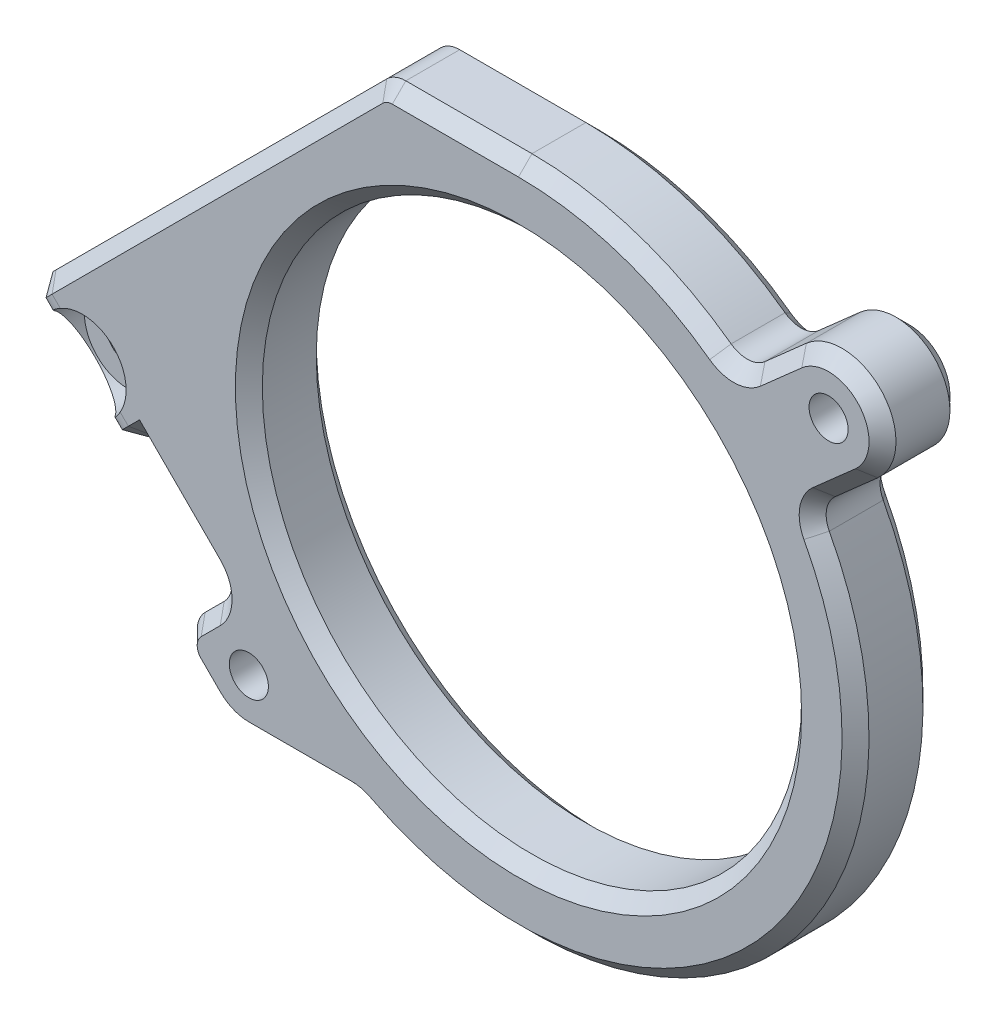
SolidWorks part; units mm, degrees
ref_plane "正面" through (0, 0, 0) normal (0, 0, 1) x (1, 0, 0)
ref_plane "平面" through (0, 0, 0) normal (0, 1, 0) x (1, 0, 0)
ref_plane "右側面" through (0, 0, 0) normal (1, 0, 0) x (0, 0, -1)
sketch "ｽｹｯﾁ1" plane through (0, 0, 0) normal (0, 0, 1) x (1, 0, 0)
  line L1 (30, -27.5) -> (-30, -27.5)
  line L2 (30, -27.5) -> (30, 27.5)
  line L3 (30, 27.5) -> (-30, 27.5)
  line L4 (-30, -27.5) -> (-30, 27.5)
  line L5 (30, -27.5) -> (-30, 27.5) construction
  line L6 (30, 27.5) -> (-30, -27.5) construction
  point P0 (0, 0)
  dimension "D1" = 55
  dimension "D2" = 60
extrude "ﾎﾞｽ - 押し出し1" add sketch "ｽｹｯﾁ1" along normal blind 6
sketch "ｽｹｯﾁ2" plane through (0, 0, 6) normal (0, 0, 1) x (1, 0, 0)
  line L0 (23, 20) -> (-20, -18)
  point P2 (0, 0)
  dimension "D1" = 18
  dimension "D2" = 20
  dimension "D3" = 43
  dimension "D4" = 38
hole_wizard "M4 すきま穴1" positions "ｽｹｯﾁ3" profile "ｽｹｯﾁ4" hole size "M4" standard "ISO"
sketch "ｽｹｯﾁ3" plane through (0, 0, 6) normal (0, 0, 1) x (1, 0, 0)
  point P0 (-20, -18)
  point P3 (23, 20)
sketch "ｽｹｯﾁ4" plane through (-20, -18, 6) normal (1, 0, 0) x (0, -1, 0)
  line L0 (0, 0) -> (0, 10)
  line L1 (0, 10) -> (1.45, 10)
  line L2 (1.45, 10) -> (1.45, 0)
  line L5 (1.45, 0) -> (0, 0)
  line L10 (0, 10) -> (-1.45, 10) construction
  line L11 (0, -6.35) -> (0, 107.95) construction
  dimension "穴の直径" = 2.9
  dimension "穴の深さ" = 10
  dimension "ﾄﾞﾘﾙ角度" = 180
sketch "ｽｹｯﾁ5" plane through (0, 0, 6) normal (0, 0, 1) x (1, 0, 0)
  circle A0 centre (0, 0) radius 20
  dimension "D1" = 40
extrude "ｶｯﾄ - 押し出し1" cut sketch "ｽｹｯﾁ5" against normal through all
sketch "ｽｹｯﾁ6" plane through (0, 0, 6) normal (0, 0, 1) x (1, 0, 0)
  line L0 (-20, -18) -> (23, 20) construction
  line L1 (23, 20) -> (-20, -18) construction
  line L2 (-22.6488, -15.0027) -> (20.3512, 22.9973)
  line L3 (-17.3512, -20.9973) -> (25.6488, 17.0027)
  line L8 (-30, 27.5) -> (-30, -27.5)
  line L9 (-30, -27.5) -> (30, -27.5)
  line L10 (30, -27.5) -> (30, 27.5)
  line L11 (30, 27.5) -> (-30, 27.5)
  line L12 (-30, 27.5) -> (-30, -27.5)
  line L13 (-30, -27.5) -> (30, -27.5)
  line L14 (30, -27.5) -> (30, 27.5)
  line L15 (30, 27.5) -> (-30, 27.5)
  circle A0 centre (0, 0) radius 20 construction
  circle A1 centre (0, 0) radius 20
  arc A2 (-22.6488, -15.0027) -> (-17.3512, -20.9973) centre (-20, -18) ccw
  arc A3 (25.6488, 17.0027) -> (20.3512, 22.9973) centre (23, 20) ccw
  circle A4 centre (0, 0) radius 25
  point P8 (1.5, 1)
  dimension "D2" = 50
  dimension "D1" = 8
  dimension "D3" = 0
extrude "ｶｯﾄ - 押し出し2" cut sketch "ｽｹｯﾁ6" against normal through all contours L13 L14 L15 L12 | A4 | A2 L3 A3 L2
sketch "ｽｹｯﾁ7" plane through (0, 0, 6) normal (0, 0, 1) x (1, 0, 0)
  line L0 (0, 25) -> (-20, 25)
  line L1 (-20, -22) -> (-21.5, -22)
  line L2 (-20, -22) -> (-20, 25)
  line L3 (-20, 25) -> (-21.5, 25)
  line L4 (-21.5, -22) -> (-21.5, 25)
  line L5 (-20, -22) -> (-11.8743, -22)
  line L8 (-21.0078, -13.5525) -> (-22.6488, -15.0027)
  line L9 (-17.3512, -20.9973) -> (-15.651, -19.4948)
  line L10 (21.2717, 13.1345) -> (25.6488, 17.0027)
  line L11 (20.3512, 22.9973) -> (16.0334, 19.1815)
  line L12 (-21.0078, -13.5525) -> (-22.6488, -15.0027)
  line L13 (-17.3512, -20.9973) -> (-15.651, -19.4948)
  line L14 (21.2717, 13.1345) -> (25.6488, 17.0027)
  line L15 (20.3512, 22.9973) -> (16.0334, 19.1815)
  arc A0 (-22.6488, -15.0027) -> (-17.3512, -20.9973) centre (-20, -18) ccw construction
  arc A5 (-22.6488, -15.0027) -> (-17.3512, -20.9973) centre (-20, -18) ccw
  arc A6 (-15.651, -19.4948) -> (21.2717, 13.1345) centre (0, 0) ccw
  arc A7 (25.6488, 17.0027) -> (20.3512, 22.9973) centre (23, 20) ccw
  arc A8 (16.0334, 19.1815) -> (-21.0078, -13.5525) centre (0, 0) ccw
  arc A9 (-22.6488, -15.0027) -> (-17.3512, -20.9973) centre (-20, -18) ccw
  arc A10 (-15.651, -19.4948) -> (21.2717, 13.1345) centre (0, 0) ccw
  arc A11 (25.6488, 17.0027) -> (20.3512, 22.9973) centre (23, 20) ccw
  arc A12 (16.0334, 19.1815) -> (-21.0078, -13.5525) centre (0, 0) ccw
  line M17 (-21.0078, -13.5525) -> (-22.6488, -15.0027)
  arc M18 (-22.6488, -15.0027) -> (-17.3512, -20.9973) centre (-20, -18) ccw
  line M19 (-17.3512, -20.9973) -> (-15.651, -19.4948)
  arc M20 (-15.651, -19.4948) -> (21.2717, 13.1345) centre (0, 0) ccw
  arc M24 (16.0334, 19.1815) -> (-21.0078, -13.5525) centre (0, 0) ccw
  dimension "D2" = 1.5
  dimension "D1" = 0
extrude "ﾎﾞｽ - 押し出し2" add sketch "ｽｹｯﾁ7" against normal up to surface (6 mm away) contours L4 L1 M18 M17 M24 | L4 L2 L3 M24 | L2 L0 M24 | L5 M18 M20 M19
sketch "ｽｹｯﾁ8" plane through (0, 0, 6) normal (0, 0, 1) x (1, 0, 0)
  line L0 (-20.9025, 25.5975) -> (-45.0784, 1.4216)
  line L1 (-45.0784, 1.4216) -> (-21.6569, -22)
  line L3 (-21.5, 12.7574) -> (-21.5, 25) construction
  line L4 (-20, -22) -> (-21.6569, -22)
  arc A1 (-22.6488, -15.0027) -> (-20, -22) centre (-20, -18) ccw construction
  point P3 (-22.5, -21)
  point P9 (-21.5, -22)
  point P10 (0, 0)
  point P11 (0, 0)
  point P13 (0, 0)
  point P15 (-21.5, -22)
  dimension "D1" = 45
extrude "ﾎﾞｽ - 押し出し3" add sketch "ｽｹｯﾁ8" against normal up to surface (6 mm away) up to face at (-3.845, 3.3122, 0)
sketch "ｽｹｯﾁ9" plane through (0, 0, 0) normal (0, 0, -1) x (-1, 0, 0)
  line L0 (32.3505, -11.3063) -> (25.2794, -4.2353)
  line L1 (22.8284, -20.8284) -> (45.0784, 1.4216) construction
  line L2 (25.2794, -4.2353) -> (38.0074, 8.4926)
  line L3 (45.0784, 1.4216) -> (21.5, 25) construction
  line M4 (22.8284, -20.8284) -> (45.0784, 1.4216)
  line M5 (45.0784, 1.4216) -> (21.5, 25)
  dimension "D1" = 10
  dimension "D2" = 18
extrude "ﾎﾞｽ - 押し出し4" add sketch "ｽｹｯﾁ9" along normal blind 4 contours L2 L0 M4 M5
sketch "ｽｹｯﾁ10" plane through (0, 0, -4) normal (0, 0, -1) x (-1, 0, 0)
  line L0 (32.3505, -11.3063) -> (25.2794, -4.2353) construction
  line L1 (25.2794, -4.2353) -> (38.0074, 8.4926) construction
  line L2 (38.0074, 8.4926) -> (21.5, 25) construction
  line L3 (21.5, 25) -> (0, 25) construction
  line L4 (-16.0334, 19.1815) -> (-20.3512, 22.9973) construction
  line L5 (-25.6488, 17.0027) -> (-21.2717, 13.1345) construction
  line L6 (11.8743, -22) -> (20, -22) construction
  line L8 (38.0074, 8.4926) -> (25.2794, -4.2353) construction
  line L9 (25.2794, -4.2353) -> (32.3505, -11.3063) construction
  line L10 (32.3505, -11.3063) -> (45.0784, 1.4216) construction
  line L11 (45.0784, 1.4216) -> (38.0074, 8.4926) construction
  line L12 (32.3505, -11.3063) -> (25.2794, -4.2353)
  line L13 (32.3505, 2.8358) -> (38.0074, 8.4926)
  line L14 (38.0074, 8.4926) -> (21.5, 25)
  line L15 (21.5, 25) -> (10.1863, 25)
  line L16 (-16.0334, 19.1815) -> (-20.3512, 22.9973)
  line L17 (-25.6488, 17.0027) -> (-21.2717, 13.1345)
  line L18 (11.8743, -22) -> (20, -22)
  line L20 (38.0074, 8.4926) -> (32.3505, 2.8358)
  line L21 (25.2794, -4.2353) -> (32.3505, -11.3063)
  line L22 (39.4216, -4.2353) -> (45.0784, 1.4216)
  line L23 (45.0784, 1.4216) -> (38.0074, 8.4926)
  line L24 (39.4216, -4.2353) -> (10.1863, 25)
  line L29 (38.0074, 8.4926) -> (25.2794, -4.2353)
  line L30 (25.2794, -4.2353) -> (32.3505, -11.3063)
  line L31 (32.3505, -11.3063) -> (45.0784, 1.4216)
  line L32 (45.0784, 1.4216) -> (38.0074, 8.4926)
  line L33 (38.0074, 8.4926) -> (32.3505, 2.8358)
  line L34 (25.2794, -4.2353) -> (32.3505, -11.3063)
  line L35 (32.3505, -11.3063) -> (45.0784, 1.4216)
  line L36 (45.0784, 1.4216) -> (38.0074, 8.4926)
  arc A0 (0, 25) -> (-16.0334, 19.1815) centre (0, 0) ccw construction
  arc A1 (-20.3512, 22.9973) -> (-25.6488, 17.0027) centre (-23, 20) ccw construction
  arc A2 (-21.2717, 13.1345) -> (11.8743, -22) centre (0, 0) ccw construction
  arc A3 (0, 25) -> (-16.0334, 19.1815) centre (0, 0) ccw
  arc A4 (-20.3512, 22.9973) -> (-25.6488, 17.0027) centre (-23, 20) ccw
  arc A5 (-21.2717, 13.1345) -> (11.8743, -22) centre (0, 0) ccw
  dimension "D1" = 8
  dimension "D2" = 0
extrude "ｶｯﾄ - 押し出し3" cut sketch "ｽｹｯﾁ10" against normal through all contours L14 L15 L24 L22 L23
sketch "ｽｹｯﾁ12" plane through (0, 0, 6) normal (0, 0, 1) x (1, 0, 0)
  line L0 (-39.4216, -4.2353) -> (-25.6569, -18)
  line L1 (-39.4216, -4.2353) -> (-35.1789, 0.0074)
  line L2 (-25.6569, -18) -> (-21.4142, -13.7574)
  line L3 (-35.1789, 0.0074) -> (-21.4142, -13.7574)
  line L4 (-39.4216, -4.2353) -> (-22.8284, -20.8284) construction
  circle A0 centre (-20, -18) radius 1.45 construction
  dimension "D1" = 4
  dimension "D2" = 6
extrude "ｶｯﾄ - 押し出し4" cut sketch "ｽｹｯﾁ12" against normal blind 6
fillet "ﾌｨﾚｯﾄ1" radius 2 3 edges at (-25.2794, -4.2353, -2) (-32.3505, 2.8358, -2) (-25.6569, -18, 3)
sketch "ｽｹｯﾁ13" plane through (0, 0, 0) normal (0, 0, 1) x (1, 0, 0)
  line L4 (-32.3505, -11.3063) -> (-28.1079, -7.0637)
  line L5 (-28.1079, -7.0637) -> (-35.1789, 0.0074)
  line L6 (-35.1789, 0.0074) -> (-39.4216, -4.2353)
  line L7 (-39.4216, -4.2353) -> (-32.3505, -11.3063)
  line L8 (-32.3505, -11.3063) -> (-28.1079, -7.0637)
  line L9 (-28.1079, -7.0637) -> (-35.1789, 0.0074)
  line L10 (-35.1789, 0.0074) -> (-39.4216, -4.2353)
  line L11 (-39.4216, -4.2353) -> (-32.3505, -11.3063)
  dimension "D1" = 0
extrude "ﾎﾞｽ - 押し出し5" add sketch "ｽｹｯﾁ13" along normal blind 6
chamfer "面取り2" distance 5 angle 45 1 edges at (-35.886, -7.7708, 6)
fillet "ﾌｨﾚｯﾄ4" radius 2 7 edges at (21.2717, 13.1345, 3) (16.0334, 19.1815, 3) (-10.1863, 25, 3) (-11.8743, -22, 3) (-21.4142, -13.7574, 3) (-35.886, -7.7708, 1) (-32.3505, -4.2353, 6)
chamfer "面取り3" distance 1 angle 45 53 edges at (-21.5307, -21.6955, 6) (-21.5307, -21.6955, 0) (-23.5355, -20.1213, 0) (-29.5221, -8.4779, -4) (-32.3505, -11.3063, -1.9142) (-35.886, -7.7708, -4) (-36.5931, -1.4069, -4) (-28.815, -0.6997, -4) (-32.3505, 2.0074, -4) (-26.1079, -4.2353, -4) (-23.5355, -15.8787, 6) (-23.5355, -15.8787, 0) (-23.5355, -20.1213, 6) (-24.8284, -18, 6) (-24.8284, -18, 0) (24.0713, 15.6086, 6) (24.0713, 15.6086, 0) (17.8053, -17.5491, 0) (17.8053, -17.5491, 6) (7.7717, 23.7613, 6) (7.7717, 23.7613, 0) (18.8154, 21.6401, 6) (18.8154, 21.6401, 0) (-39.4216, -4.2353, -1.9142) (-37.6538, -2.4675, 3.5) (-23.0362, 12.1501, 6) (-22.2684, 12.9179, 0) (-35.8414, -0.6552, 5.8478) (-39.3139, -4.1276, 0.9369) (-25.4681, -9.7034, 0) (-4.6789, 25, 0) (-16.1847, -22, 0) (-10.1232, 24.8478, 0) (-28.1685, -7.1244, 6) (-25.4681, -9.7034, 6) (-10.1232, 24.8478, 6) (-30.5827, -9.5386, 3.5) (-28.7704, -7.7262, 5.8478) (-32.2429, -11.1987, 0.9369) (21.8499, 13.0707, 0) (21.8499, 13.0707, 6) (16.0467, 19.7836, 0) (16.0467, 19.7836, 6) (-11.8979, -22.0563, 6) (-11.8979, -22.0563, 0) (-22.2426, -13.7574, 6) (-22.2426, -13.7574, 0) (20, 0, 0) (20, 0, 6) (25.9973, 22.6488, 0) (25.9973, 22.6488, 6) (-16.1847, -22, 6) (-4.6789, 25, 6)
sketch "ｽｹｯﾁ14" plane through (0, 0, 6) normal (0, 0, 1) x (1, 0, 0)
  line L0 (-31.7647, -3.6495) -> (-32.3505, -4.2353)
  line L11 (-34.5931, -0.8211) -> (-28.9363, -6.4779)
  line L21 (-34.5931, -0.8211) -> (-28.9363, -6.4779)
  line L50 (-33.0576, -10.5992) -> (-38.7145, -4.9424) construction
  line L87 (-10.065, 23.7071) -> (-34.5931, -0.8211)
  line L88 (-10.065, 23.7071) -> (-34.5931, -0.8211)
  line L89 (-28.9363, -6.4779) -> (-28.1079, -5.6495)
  line L90 (-28.9363, -6.4779) -> (-28.1079, -5.6495)
  line L91 (-28.1079, -5.6495) -> (-22.1213, -11.636)
  line L92 (-28.1079, -5.6495) -> (-22.1213, -11.636)
  line L93 (-22.1213, -15.8787) -> (-23.5355, -17.2929)
  line L94 (-22.1213, -15.8787) -> (-23.5355, -17.2929)
  line L95 (-23.5355, -18.7071) -> (-22.1213, -20.1213)
  line L96 (-23.5355, -18.7071) -> (-22.1213, -20.1213)
  line L97 (-20, -21) -> (-12.3693, -21)
  line L98 (-20, -21) -> (-12.3693, -21)
  line L99 (21.8316, 14.9639) -> (24.9866, 17.752)
  line L100 (21.8316, 14.9639) -> (24.9866, 17.752)
  line L101 (21.0134, 22.248) -> (17.9417, 19.5335)
  line L102 (21.0134, 22.248) -> (17.9417, 19.5335)
  line L103 (0, 24) -> (-9.3579, 24)
  line L104 (0, 24) -> (-9.3579, 24)
  arc A94 (-9.3579, 24) -> (-10.065, 23.7071) centre (-9.3579, 23) ccw
  arc A95 (-9.3579, 24) -> (-10.065, 23.7071) centre (-9.3579, 23) ccw
  arc A96 (-22.1213, -15.8787) -> (-22.1213, -11.636) centre (-24.2426, -13.7574) ccw
  arc A97 (-22.1213, -15.8787) -> (-22.1213, -11.636) centre (-24.2426, -13.7574) ccw
  arc A98 (-23.5355, -17.2929) -> (-23.5355, -18.7071) centre (-22.8284, -18) ccw
  arc A99 (-23.5355, -17.2929) -> (-23.5355, -18.7071) centre (-22.8284, -18) ccw
  arc A100 (-10.9949, -21.3333) -> (-12.3693, -21) centre (-12.3693, -24) ccw
  arc A101 (-10.9949, -21.3333) -> (-12.3693, -21) centre (-12.3693, -24) ccw
  arc A102 (-10.9949, -21.3333) -> (21.1717, 11.303) centre (0, 0) ccw
  arc A103 (-10.9949, -21.3333) -> (21.1717, 11.303) centre (0, 0) ccw
  arc A104 (21.8316, 14.9639) -> (21.1717, 11.303) centre (23.8182, 12.7159) ccw
  arc A105 (21.8316, 14.9639) -> (21.1717, 11.303) centre (23.8182, 12.7159) ccw
  arc A106 (24.9866, 17.752) -> (21.0134, 22.248) centre (23, 20) ccw
  arc A107 (24.9866, 17.752) -> (21.0134, 22.248) centre (23, 20) ccw
  arc A108 (14.1824, 19.3613) -> (17.9417, 19.5335) centre (15.9552, 21.7815) ccw
  arc A109 (14.1824, 19.3613) -> (17.9417, 19.5335) centre (15.9552, 21.7815) ccw
  arc A110 (14.1824, 19.3613) -> (0, 24) centre (0, 0) ccw
  arc A111 (14.1824, 19.3613) -> (0, 24) centre (0, 0) ccw
  arc A112 (-22.1213, -20.1213) -> (-20, -21) centre (-20, -18) ccw
  arc A113 (-22.1213, -20.1213) -> (-20, -21) centre (-20, -18) ccw
  point P16 (0, 0)
  dimension "D2" = 5
  dimension "D1" = 0
hole_wizard "M3 六角穴付き頭ねじ用座ぐり穴2" positions "ｽｹｯﾁ19" profile "ｽｹｯﾁ20" counterbore size "M3" standard "ISO"
sketch "ｽｹｯﾁ19" plane through (0, 0, 6) normal (0, 0, 1) x (1, 0, 0)
  point P0 (-32.3505, -4.2353)
sketch "ｽｹｯﾁ20" plane through (-32.3505, -4.2353, 6) normal (1, 0, 0) x (0, -1, 0)
  line L0 (0, 0) -> (0, 10.9914)
  line L1 (0, 10.9914) -> (1.65, 10)
  line L2 (1.65, 10) -> (1.65, 3.4)
  line L3 (1.65, 3.4) -> (3.25, 3.4)
  line L4 (3.25, 3.4) -> (3.25, 0)
  line L5 (3.25, 0) -> (0, 0)
  line L10 (0, 10.9914) -> (-1.65, 10) construction
  line L11 (0, -6.35) -> (0, 107.95) construction
  dimension "穴の直径" = 3.3
  dimension "穴の深さ" = 10
  dimension "座ぐり穴の直径" = 6.5
  dimension "座ぐり穴の深さ" = 3.4
  dimension "ﾄﾞﾘﾙ角度" = 118
